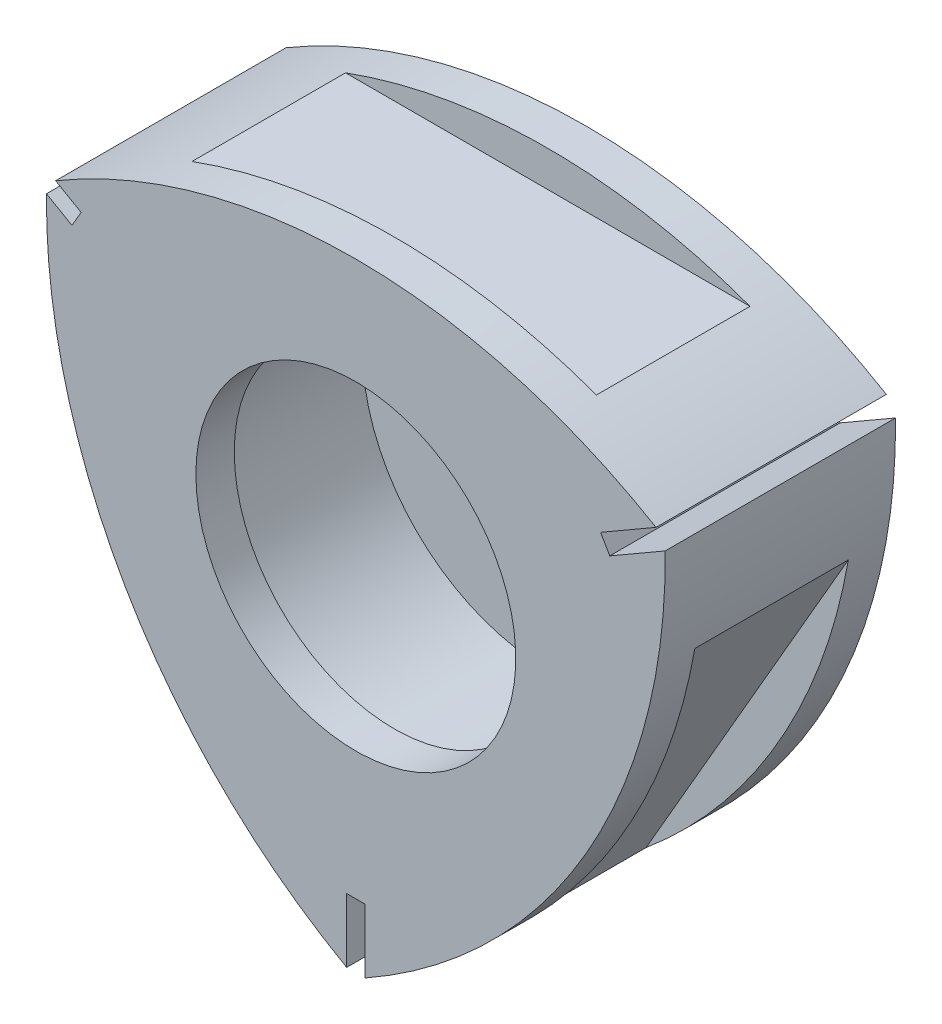
SolidWorks part; units mm, degrees
extrude "Base-Extrude" add sketch "rotor profile" along normal blind 18
sketch "rotor profile" plane through (0, 0, 0) normal (0, 0, 1) x (1, 0, 0)
  line L0 (0, -31.6325) -> (0, 0) construction
  line L5 (0, 0) -> (0, 28.1893) construction
  line L6 (-23.8157, 13.75) -> (-23.4583, 14.369) construction
  line L7 (-23.8157, 13.75) -> (-24.1731, 13.131) construction
  line L8 (-24.1731, 13.131) -> (-22.1812, 11.981)
  line L9 (-23.4583, 14.369) -> (-21.4664, 13.219)
  line L10 (-21.8238, 12.6) -> (-21.4664, 13.219)
  line L11 (-21.8238, 12.6) -> (-22.1812, 11.981)
  line L12 (23.8157, 13.75) -> (23.4583, 14.369) construction
  line L13 (23.8157, 13.75) -> (24.1731, 13.131) construction
  line L14 (19.4856, 11.25) -> (19.843, 10.631)
  line L15 (19.4856, 11.25) -> (19.1282, 11.869)
  line L16 (23.4583, 14.369) -> (19.1282, 11.869)
  line L17 (24.1731, 13.131) -> (19.843, 10.631)
  line L18 (0, -27.5) -> (0.7148, -27.5) construction
  line L19 (0, -27.5) -> (-0.7148, -27.5) construction
  line L20 (0, -22.5) -> (0.7148, -22.5)
  line L21 (0, -22.5) -> (-0.7148, -22.5)
  line L22 (-0.7148, -27.5) -> (-0.7148, -22.5)
  line L23 (0.7148, -27.5) -> (0.7148, -22.5)
  line L24 (0, -25.2) -> (-23.8157, 13.75) construction
  line L25 (0, -25.2) -> (23.8157, 13.75) construction
  arc A0 (18.0133, -10.4) -> (24.1731, 13.131) centre (-21.8238, 12.6) ccw
  arc A1 (0, 20.8) -> (-23.4583, 14.369) centre (0, -25.2) ccw
  arc A2 (-18.0133, -10.4) -> (-0.7148, -27.5) centre (21.8238, 12.6) ccw
  arc A3 (0.7148, -27.5) -> (18.0133, -10.4) centre (-21.8238, 12.6) ccw
  arc A4 (23.4583, 14.369) -> (0, 20.8) centre (0, -25.2) ccw
  arc A5 (-18.0133, -10.4) -> (-24.1731, 13.131) centre (21.8238, 12.6) cw
  point P6 (-18.0133, -10.4)
  point P8 (0, 0)
  point P9 (18.0133, -10.4)
  point P10 (0, -25.2)
  point P13 (0, -22.5)
  point P15 (21.8238, 12.6)
  point P18 (19.4856, 11.25)
  point P20 (-21.8238, 12.6)
  point P23 (0, 20.8)
  point P27 (0, -27.5)
  point P28 (-23.8157, 13.75)
  point P29 (23.8157, 13.75)
  point P30 (-19.4856, 11.25)
  dimension "D4" = 45.654
  dimension "D3" = 31.443
  dimension "D1" = 46
  dimension "D2" = 31.443
extrude "Cut-Extrude1" cut sketch "combustion chamber profile" against normal blind 12
sketch "combustion chamber profile" plane through (0, 0, 3) normal (0, 0, -1) x (-1, 0, 0)
  line L0 (0, 0) -> (-15.5885, -9) construction
  line L1 (18, 21) -> (18, 18)
  line L2 (-18, 21) -> (18, 21)
  line L3 (-18, 18) -> (-18, 21)
  line L4 (0, 18) -> (-18, 18)
  line L5 (0, 0) -> (0, 18) construction
  line L6 (-9.1865, -26.0885) -> (-27.1865, 5.0885)
  line L7 (-27.1865, 5.0885) -> (-24.5885, 6.5885)
  line L8 (-24.5885, 6.5885) -> (-15.5885, -9)
  line L9 (-15.5885, -9) -> (-6.5885, -24.5885)
  line L10 (-6.5885, -24.5885) -> (-9.1865, -26.0885)
  line L11 (18, 18) -> (0, 18)
  line L16 (27.1865, 5.0885) -> (9.1865, -26.0885)
  line L17 (9.1865, -26.0885) -> (6.5885, -24.5885)
  line L18 (6.5885, -24.5885) -> (15.5885, -9)
  line L19 (15.5885, -9) -> (24.5885, 6.5885)
  line L20 (24.5885, 6.5885) -> (27.1865, 5.0885)
  line L21 (0, 0) -> (15.5885, -9) construction
  circle A0 centre (0, 0) radius 14.5
  point P1 (0, 0)
  dimension "D16" = 29
  dimension "D2" = 120
  dimension "D3" = 120
  dimension "D4" = 18
  dimension "D5" = 18
  dimension "D6" = 3
  dimension "D7" = 3
  dimension "D8" = 18
  dimension "D9" = 18
  dimension "D10" = 18
  dimension "D11" = 18
  dimension "D12" = 18
  dimension "D13" = 3
  dimension "D14" = 18
  dimension "D15" = 18
ref_plane "Front" through (0, 0, 0) normal (0, 0, 1) x (1, 0, 0)
ref_plane "Top" through (0, 0, 0) normal (0, 1, 0) x (1, 0, 0)
ref_plane "Right" through (0, 0, 0) normal (1, 0, 0) x (0, 0, -1)
ref_plane "Plane 3mm offest" through (0, 0, 3) normal (0, 0, -1) x (-1, 0, 0)
ref_plane "Plane 18mm offest" through (0, 0, 18) normal (0, 0, -1) x (-1, 0, 0)
sketch "Sketch5" plane through (0, 0, 18) normal (0, 0, -1) x (-1, 0, 0)
  circle A0 centre (0, 0) radius 12.5
  dimension "D1" = 25
sketch "Sketch6" plane through (0, 0, 18) normal (0, 0, -1) x (-1, 0, 0)
  circle A0 centre (0, 0) radius 12.5
extrude "Cut-Extrude5" cut sketch "Sketch6" along normal blind 3
ref_plane "Plane1" through (0, 0, 18) normal (0, 0, 1) x (1, 0, 0)
